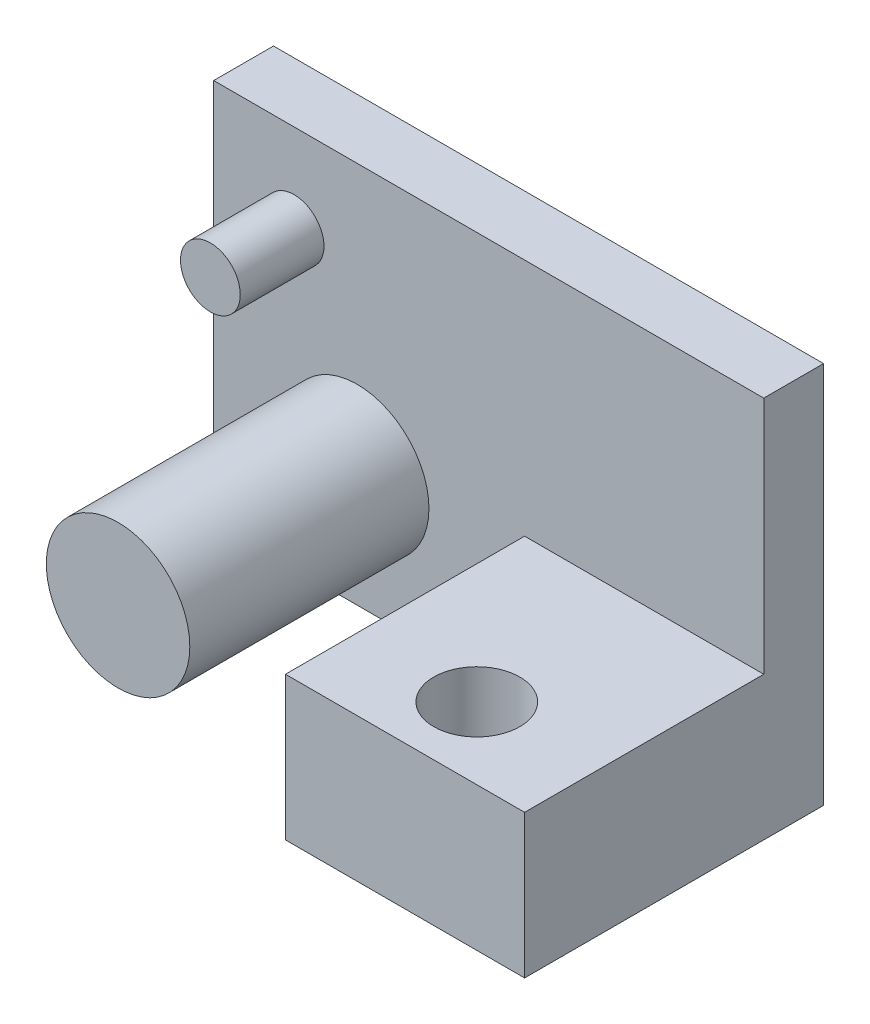
SolidWorks part; units mm, degrees
ref_plane "Front Plane" through (0, 0, 0) normal (0, 0, 1) x (1, 0, 0)
ref_plane "Top Plane" through (0, 0, 0) normal (0, 1, 0) x (1, 0, 0)
ref_plane "Right Plane" through (0, 0, 0) normal (1, 0, 0) x (0, 0, -1)
sketch "Sketch1" plane through (0, 0, 0) normal (0, 0, 1) x (1, 0, 0)
  line L0 (-35.6903, -28.2897) -> (-35.6903, -18.2897)
  line L1 (-35.6903, -28.2897) -> (-7.6903, -28.2897)
  line L2 (-7.6903, 1.7103) -> (-17.6903, 1.7103)
  line L3 (-7.6903, -28.2897) -> (-7.6903, 1.7103)
  line L4 (-35.6903, -18.2897) -> (-17.6903, 1.7103)
extrude "Boss-Extrude1" add sketch "Sketch1" along normal blind 2.5
sketch "Sketch2" plane through (0, 0, 2.5) normal (0, 0, 1) x (1, 0, 0)
  line L1 (-35.6903, -28.2897) -> (-7.6903, -28.2897) construction
  line L2 (-7.6903, -28.2897) -> (-7.6903, 1.7103) construction
  circle A0 centre (-11.6903, -2.6697) radius 1.25
  dimension "D1" = 4
  dimension "D2" = 25.62
extrude "Boss-Extrude2" add sketch "Sketch2" along normal blind 3.5
sketch "Sketch3" plane through (0, 0, 2.5) normal (0, 0, 1) x (1, 0, 0)
  line L0 (-35.6903, -28.2897) -> (-7.6903, -28.2897) construction
  line L1 (-35.6903, -18.2897) -> (-35.6903, -28.2897) construction
  circle A0 centre (-31.6903, -23.2897) radius 3
  dimension "D1" = 5
  dimension "D2" = 4
extrude "Boss-Extrude3" add sketch "Sketch3" along normal blind 10
sketch "Sketch4" plane through (0, 0, 2.5) normal (0, 0, 1) x (1, 0, 0)
  line L0 (-35.6903, -28.2897) -> (-7.6903, -28.2897) construction
  line L1 (-24.6903, -28.2897) -> (-14.6903, -28.2897)
  line L2 (-24.6903, -28.2897) -> (-24.6903, -22.2897)
  line L3 (-24.6903, -22.2897) -> (-14.6903, -22.2897)
  line L4 (-14.6903, -28.2897) -> (-14.6903, -22.2897)
  line L5 (-35.6903, -18.2897) -> (-35.6903, -28.2897) construction
  dimension "D1" = 10
  dimension "D2" = 11
  dimension "D3" = 6
extrude "Boss-Extrude4" add sketch "Sketch4" along normal blind 10
sketch "Sketch5" plane through (0, -22.2897, 0) normal (0, 1, 0) x (1, 0, 0)
  line L0 (-24.6903, -12.5) -> (-24.6903, -2.5) construction
  line L1 (-14.6903, -12.5) -> (-24.6903, -12.5) construction
  circle A0 centre (-19.6903, -9.5) radius 1.8
  dimension "D1" = 5
  dimension "D2" = 3
extrude "Cut-Extrude1" cut sketch "Sketch5" against normal blind 10
sketch "Sketch6" plane through (0, 0, 2.5) normal (0, 0, 1) x (1, 0, 0)
  line L0 (-35.6903, -28.2897) -> (-39.6903, -28.2897)
  line L1 (-39.6903, -28.2897) -> (-39.6903, -12.2897)
  line L2 (-39.6903, -12.2897) -> (-30.2903, -12.2897)
  line L3 (-17.6903, 1.7103) -> (-35.6903, -18.2897) construction
  line L4 (-30.2903, -12.2897) -> (-35.6903, -18.2897)
  line L5 (-35.6903, -18.2897) -> (-35.6903, -28.2897)
extrude "Boss-Extrude5" add sketch "Sketch6" against normal blind 2.5
sketch "Sketch9" plane through (0, 0, 6) normal (0, 0, 1) x (1, 0, 0)
  line L1 (-14.6903, -28.2897) -> (-7.6903, -28.2897)
  line L2 (-14.6903, -28.2897) -> (-14.6903, 1.7103)
  line L3 (-14.6903, 1.7103) -> (-7.6903, 1.7103)
  line L4 (-7.6903, -28.2897) -> (-7.6903, 1.7103)
extrude "Cut-Extrude2" cut sketch "Sketch9" against normal blind 10
sketch "Sketch10" plane through (0, 0, 2.5) normal (0, 0, 1) x (1, 0, 0)
  line L1 (-30.2903, -12.2897) -> (-14.6903, -12.2897)
  line L2 (-30.2903, -12.2897) -> (-30.2903, 1.7103)
  line L3 (-30.2903, 1.7103) -> (-14.6903, 1.7103)
  line L4 (-14.6903, -12.2897) -> (-14.6903, 1.7103)
extrude "Cut-Extrude3" cut sketch "Sketch10" against normal blind 10
sketch "Sketch11" plane through (0, 0, 2.5) normal (0, 0, 1) x (1, 0, 0)
  line L0 (-14.6903, -12.2897) -> (-39.6903, -12.2897) construction
  line L1 (-39.6903, -28.2897) -> (-37.6903, -28.2897)
  line L2 (-39.6903, -28.2897) -> (-39.6903, -12.2897)
  line L3 (-39.6903, -12.2897) -> (-37.6903, -12.2897)
  line L4 (-37.6903, -28.2897) -> (-37.6903, -12.2897)
  dimension "D1" = 2
extrude "Cut-Extrude4" cut sketch "Sketch11" against normal blind 10
sketch "Sketch12" plane through (0, 0, 2.5) normal (0, 0, 1) x (1, 0, 0)
  line L0 (-14.6903, -12.2897) -> (-14.6903, -22.2897) construction
  line L1 (-14.6903, -12.2897) -> (-37.6903, -12.2897) construction
  circle A0 centre (-34.3303, -15.9897) radius 1.25
  dimension "D1" = 19.64
  dimension "D2" = 3.7
extrude "Boss-Extrude6" add sketch "Sketch12" along normal blind 3.5
sketch "Sketch13" plane through (0, 0, 2.5) normal (0, 0, 1) x (1, 0, 0)
  line L1 (-37.6903, -28.2897) -> (-35.6903, -28.2897)
  line L2 (-37.6903, -28.2897) -> (-37.6903, -25.2897)
  line L3 (-37.6903, -25.2897) -> (-35.6903, -25.2897)
  line L4 (-35.6903, -28.2897) -> (-35.6903, -25.2897)
  dimension "D1" = 2
  dimension "D2" = 3
extrude "Cut-Extrude5" cut sketch "Sketch13" against normal blind 10
